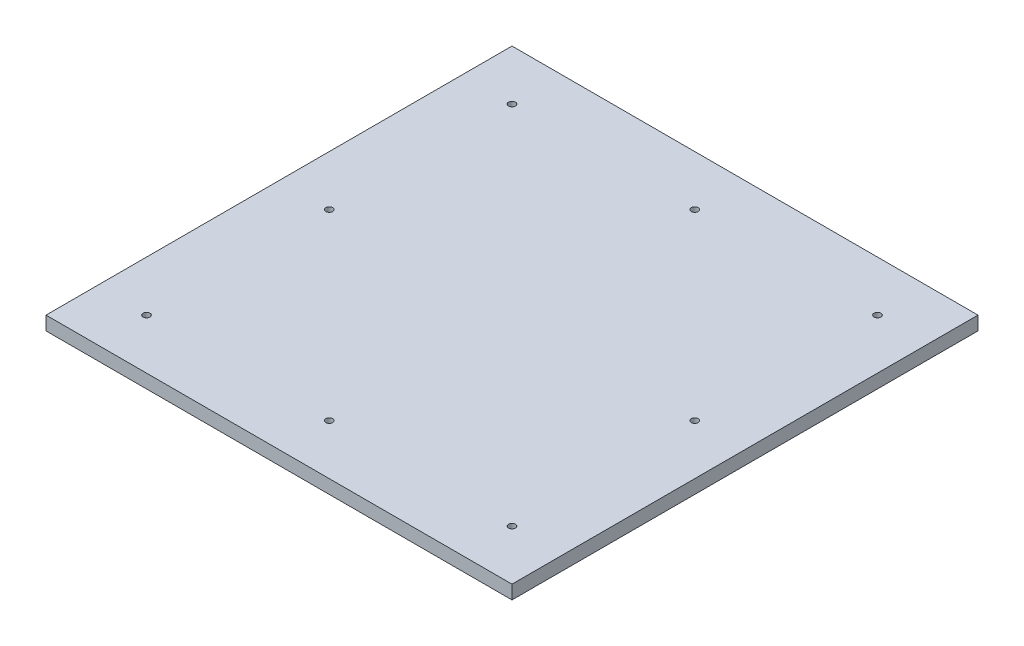
SolidWorks part; units mm, degrees
ref_plane "Front Plane" through (0, 0, 0) normal (0, 0, 1) x (1, 0, 0)
ref_plane "Top Plane" through (0, 0, 0) normal (0, 1, 0) x (1, 0, 0)
ref_plane "Right Plane" through (0, 0, 0) normal (1, 0, 0) x (0, 0, -1)
sketch "Sketch1" plane through (0, 0, 0) normal (0, 1, 0) x (1, 0, 0)
  line L1 (0, 0) -> (647.7, 0)
  line L2 (0, 0) -> (0, -647.7)
  line L3 (0, -647.7) -> (647.7, -647.7)
  line L4 (647.7, 0) -> (647.7, -647.7)
  circle A0 centre (69.85, -69.85) radius 4.7625
  circle A1 centre (323.85, -69.85) radius 4.7625
  circle A2 centre (577.85, -69.85) radius 4.7625
  circle A3 centre (69.85, -323.85) radius 4.7625
  circle A4 centre (577.85, -323.85) radius 4.7625
  circle A6 centre (69.85, -577.85) radius 4.7625
  circle A7 centre (577.85, -577.85) radius 4.7625
  circle A8 centre (323.85, -577.85) radius 4.7625
  dimension "D3" = 9.525
  dimension "D4" = 69.85
  dimension "D5" = 69.85
  dimension "D1" = 647.7
  dimension "D2" = 647.7
  dimension "D6" = 3
extrude "Boss-Extrude1" add sketch "Sketch1" along normal blind 19.05
